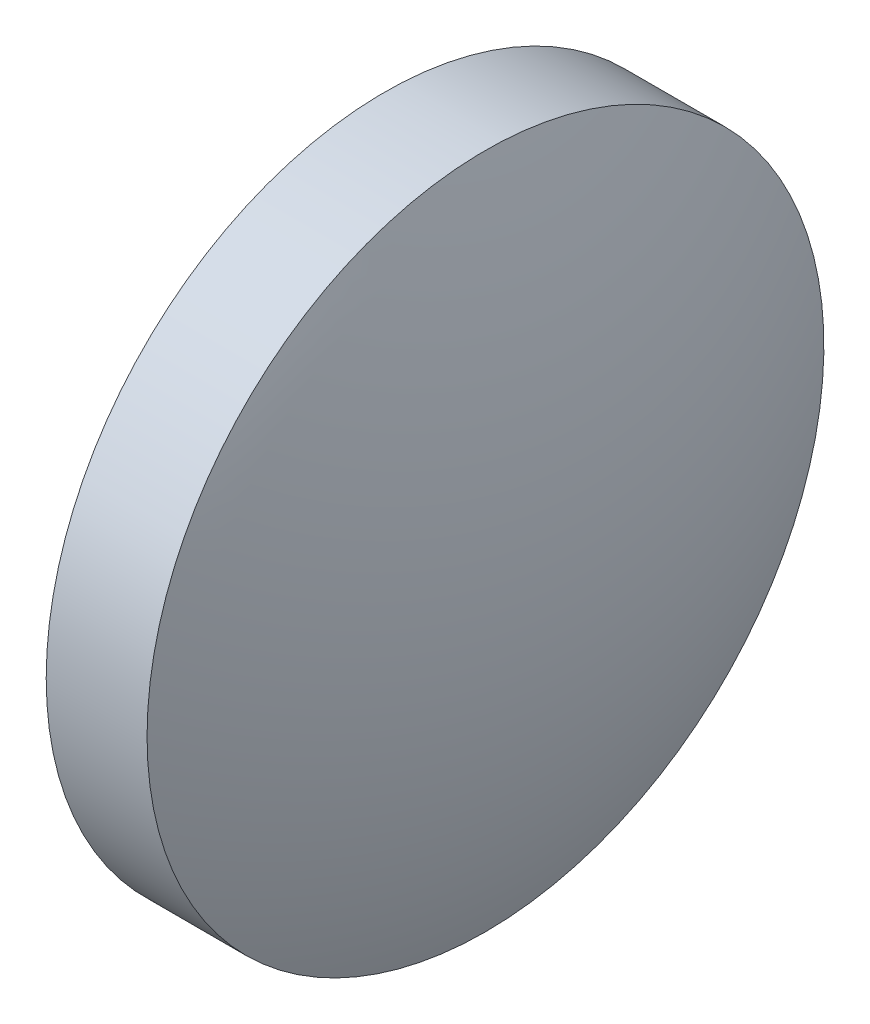
SolidWorks part; units mm, degrees
ref_plane "前视基准面" through (0, 0, 0) normal (0, 0, 1) x (1, 0, 0)
ref_plane "上视基准面" through (0, 0, 0) normal (0, 1, 0) x (1, 0, 0)
ref_plane "右视基准面" through (0, 0, 0) normal (1, 0, 0) x (0, 0, -1)
sketch "草图1" plane through (0, 0, 0) normal (0, 0, 1) x (1, 0, 0)
  line L0 (661.3522, 171.2161) -> (666.9527, 171.2161) construction
  line L1 (662.1499, 171.2161) -> (662.1499, 176.2161)
  line L2 (664.6499, 171.2161) -> (662.1499, 171.2161)
  line L5 (662.1499, 176.2161) -> (663.6399, 176.2161)
  arc A0 (664.6499, 171.2161) -> (663.6399, 176.2161) centre (651.7686, 171.2161) ccw
revolve "旋转1" add sketch "草图1" angle 360 about L0
